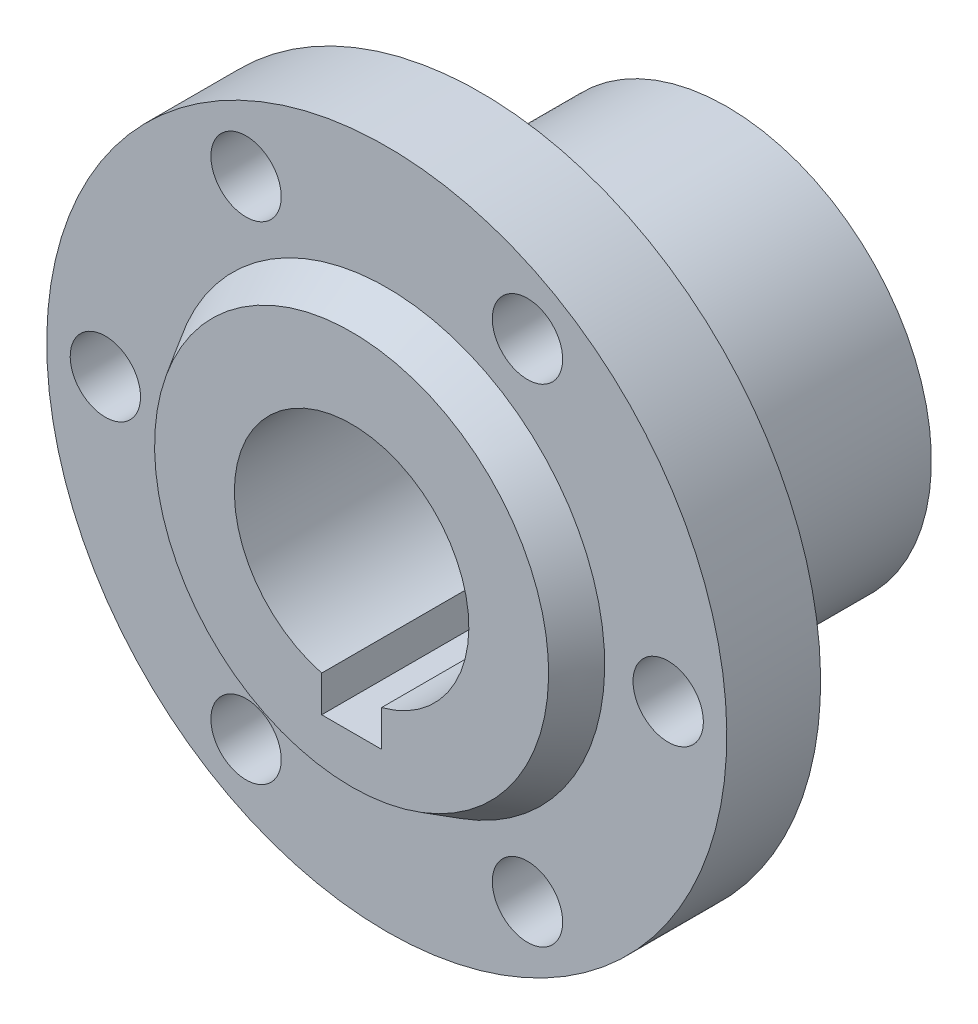
SolidWorks part; units mm, degrees
ref_plane "Front Plane" through (0, 0, 0) normal (0, 0, 1) x (1, 0, 0)
ref_plane "Top Plane" through (0, 0, 0) normal (0, 1, 0) x (1, 0, 0)
ref_plane "Right Plane" through (0, 0, 0) normal (1, 0, 0) x (0, 0, -1)
sketch "Sketch1" plane through (0, 0, 0) normal (1, 0, 0) x (0, 0, -1)
  line L0 (-11, 0) -> (21, 0) construction
  line L1 (21, 0) -> (21, 17.45) construction
  line L2 (21, 17.45) -> (7.03, 17.45)
  line L3 (7.03, 17.45) -> (7.03, 18.5)
  line L4 (7.03, 18.5) -> (0, 18.5)
  line L6 (0, 18.5) -> (0, 29)
  line L8 (0, 29) -> (-8, 29)
  line L9 (-8, 29) -> (-8, 18.5862)
  line L11 (-8, 18.5862) -> (-11, 16.8032)
  line L12 (-11, 16.8032) -> (-11, 0) construction
  line L13 (-11, 10) -> (21, 10)
  line L14 (-11, 10) -> (-11, 16.8032)
  line L15 (21, 10) -> (21, 17.45)
  dimension "D1" = 10
  dimension "D2" = 29
  dimension "D3" = 18.5
  dimension "D4" = 17.45
  dimension "D5" = 13.97
  dimension "D6" = 6.8032
  dimension "D7" = 8
revolve "Revolve1" add sketch "Sketch1" angle 360 about L0
sketch "Sketch2" plane through (0, 0, 0) normal (0, 0, 1) x (1, 0, 0)
  line L0 (0, 0) -> (0, -12.75) construction
  line L1 (-2.55, -12.75) -> (2.55, -12.75)
  line L2 (-2.55, -12.75) -> (-2.55, -9.6694)
  line L3 (2.55, -12.75) -> (2.55, -9.6694)
  circle A0 centre (0, 0) radius 10 construction
  arc A1 (-2.55, -9.6694) -> (2.55, -9.6694) centre (0, 0) ccw
  point P6 (0, -12.75)
  point P12 (2.55, -12.75)
  dimension "D1" = 12.75
  dimension "D2" = 5.1
extrude "Cut-Extrude1" cut sketch "Sketch2" against normal through all both and the other way through all
sketch "Sketch3" plane through (0, 0, 0) normal (0, 0, -1) x (-1, 0, 0)
  circle A0 centre (0, 0) radius 24 construction
  circle A1 centre (-24, 0) radius 3
  circle A2 centre (0, 0) radius 24 construction
  circle A3 centre (-12, 20.7846) radius 3
  circle A4 centre (0, 0) radius 24 construction
  circle A5 centre (12, 20.7846) radius 3
  circle A6 centre (0, 0) radius 24 construction
  circle A7 centre (24, 0) radius 3
  circle A8 centre (0, 0) radius 24 construction
  circle A9 centre (12, -20.7846) radius 3
  circle A10 centre (0, 0) radius 24 construction
  circle A11 centre (-12, -20.7846) radius 3
  dimension "D1" = 6
  dimension "D3" = 48
  dimension "D2" = 6
extrude "Cut-Extrude2" cut sketch "Sketch3" against normal through all both and the other way through all
